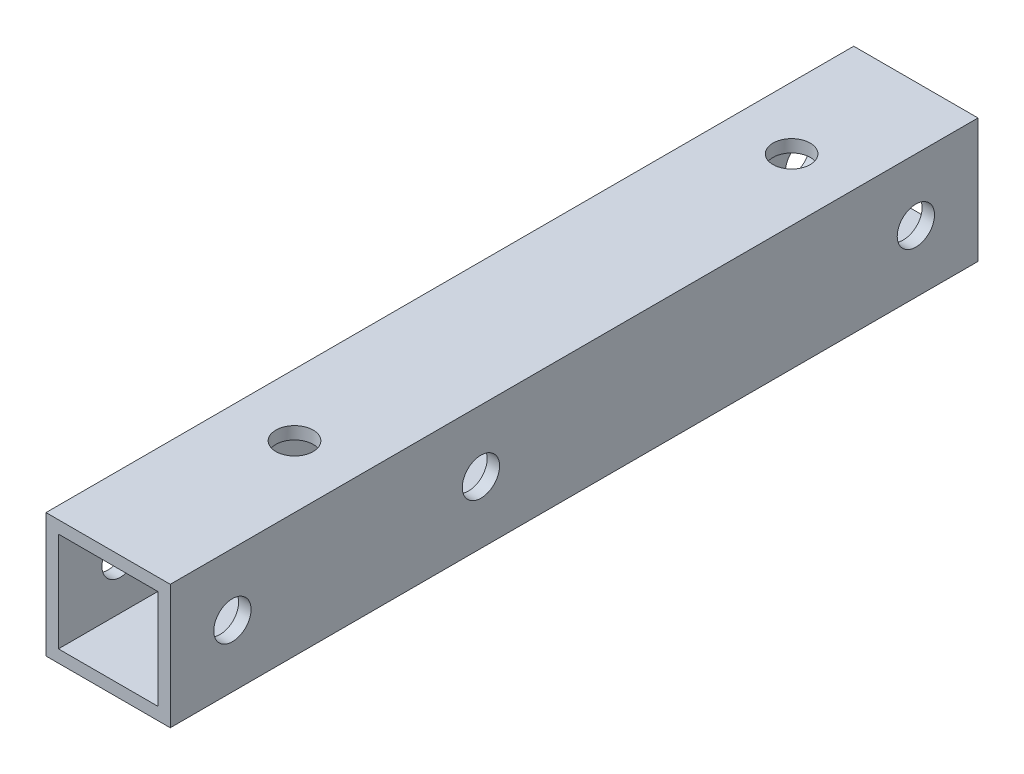
SolidWorks part; units mm, degrees
material "6063-O"
ref_plane "前视基准面" through (0, 0, 0) normal (0, 0, 1) x (1, 0, 0)
ref_plane "上视基准面" through (0, 0, 0) normal (0, 1, 0) x (1, 0, 0)
ref_plane "右视基准面" through (0, 0, 0) normal (1, 0, 0) x (0, 0, -1)
other "Configuration Table"
sketch "草图1" plane through (0, 0, 0) normal (0, 0, 1) x (1, 0, 0)
  line L1 (-5, 5) -> (5, 5)
  line L2 (-5, 5) -> (-5, -5)
  line L3 (-5, -5) -> (5, -5)
  line L4 (5, 5) -> (5, -5)
  line L5 (-5, 5) -> (5, -5) construction
  line L6 (-5, -5) -> (5, 5) construction
  point P4 (0, 0)
  dimension "D1" = 10
  dimension "D2" = 10
extrude "拉伸-薄壁1" add sketch "草图1" along normal blind 65 thin
sketch "草图2" plane through (-5, 0, 0) normal (-1, 0, 0) x (0, 0, 1)
  line L0 (0, 0) -> (65, 0) construction
  line L1 (0, 5) -> (0, -5) construction
  line L2 (65, 5) -> (65, -5) construction
  circle A0 centre (40, 0) radius 1.5
  circle A1 centre (60, 0) radius 1.5
  circle A2 centre (5, 0) radius 1.5
  dimension "D1" = 3
  dimension "D2" = 5
  dimension "D3" = 20
  dimension "D4" = 35
extrude "切除-拉伸1" cut sketch "草图2" against normal through all
sketch "草图5" plane through (0, 5, 0) normal (0, 1, 0) x (1, 0, 0)
  line L0 (0, 0) -> (0, -65) construction
  line L1 (5, 0) -> (-5, 0) construction
  line L2 (5, -65) -> (-5, -65) construction
  circle A0 centre (0, -10) radius 1.5
  circle A1 centre (0, -50) radius 1.5
  dimension "D2" = 3
  dimension "D3" = 40
  dimension "D4" = 15
extrude "切除-拉伸2" cut sketch "草图5" against normal through all
sketch "草图6" plane through (0, 5, 0) normal (0, 1, 0) x (1, 0, 0)
  circle A0 centre (0, -10) radius 3.5
  circle A1 centre (0, -50) radius 3.5
  dimension "D1" = 7
extrude "切除-拉伸3" cut sketch "草图6" against normal blind 5 from offset 5
